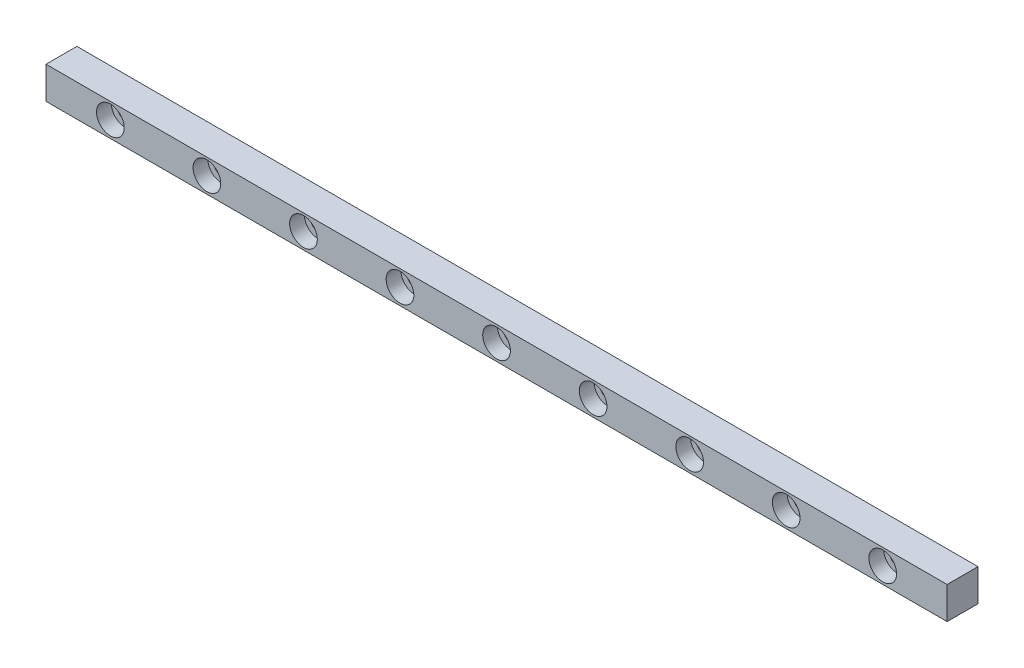
SolidWorks part; units mm, degrees
ref_plane "前视基准面" through (0, 0, 0) normal (0, 0, 1) x (1, 0, 0)
ref_plane "上视基准面" through (0, 0, 0) normal (0, 1, 0) x (1, 0, 0)
ref_plane "右视基准面" through (0, 0, 0) normal (1, 0, 0) x (0, 0, -1)
sketch "草图1" plane through (0, 0, 0) normal (0, 0, 1) x (1, 0, 0)
  line L1 (70, -2.5) -> (-70, -2.5)
  line L2 (70, -2.5) -> (70, 2.5)
  line L3 (70, 2.5) -> (-70, 2.5)
  line L4 (-70, -2.5) -> (-70, 2.5)
  line L5 (70, -2.5) -> (-70, 2.5) construction
  line L6 (70, 2.5) -> (-70, -2.5) construction
  point P0 (0, 0)
  dimension "D1" = 5
  dimension "D2" = 140
extrude "凸台-拉伸1" add sketch "草图1" along normal blind 4.8
hole_wizard "打孔尺寸(%根据)内六角圆柱头螺钉的类型1" positions "草图4" profile "草图3" counterbore size "M2" standard "GB"
sketch "草图4" plane through (0, 0, 4.8) normal (0, 0, 1) x (1, 0, 0)
  line L0 (-70, 2.5) -> (-70, -2.5) construction
  line L1 (-60, 0) -> (0.9248, 0) construction
  point P14 (-60, 0)
  point P27 (-45, 0)
  point P28 (-30, 0)
  point P29 (-15, 0)
  point P30 (0, 0)
  point P31 (15, 0)
  point P32 (30, 0)
  point P33 (45, 0)
  point P34 (60, 0)
  dimension "D1" = 10
  dimension "D3" = 90
  dimension "D2" = 9
sketch "草图3" plane through (-60, 0, 4.8) normal (1, 0, 0) x (0, -1, 0)
  line L0 (0, 0) -> (0, 5.921)
  line L1 (0, 5.921) -> (1.2, 5.2)
  line L2 (1.2, 5.2) -> (1.2, 2.3)
  line L3 (1.2, 2.3) -> (2.15, 2.3)
  line L4 (2.15, 2.3) -> (2.15, 0)
  line L5 (2.15, 0) -> (0, 0)
  line L10 (0, 5.921) -> (-1.2, 5.2) construction
  line L11 (0, -6.35) -> (0, 107.95) construction
  dimension "孔直径" = 2.4
  dimension "孔深度" = 5.2
  dimension "柱形沉头孔直径" = 4.3
  dimension "柱形沉头孔深度" = 2.3
  dimension "导头角度" = 118
